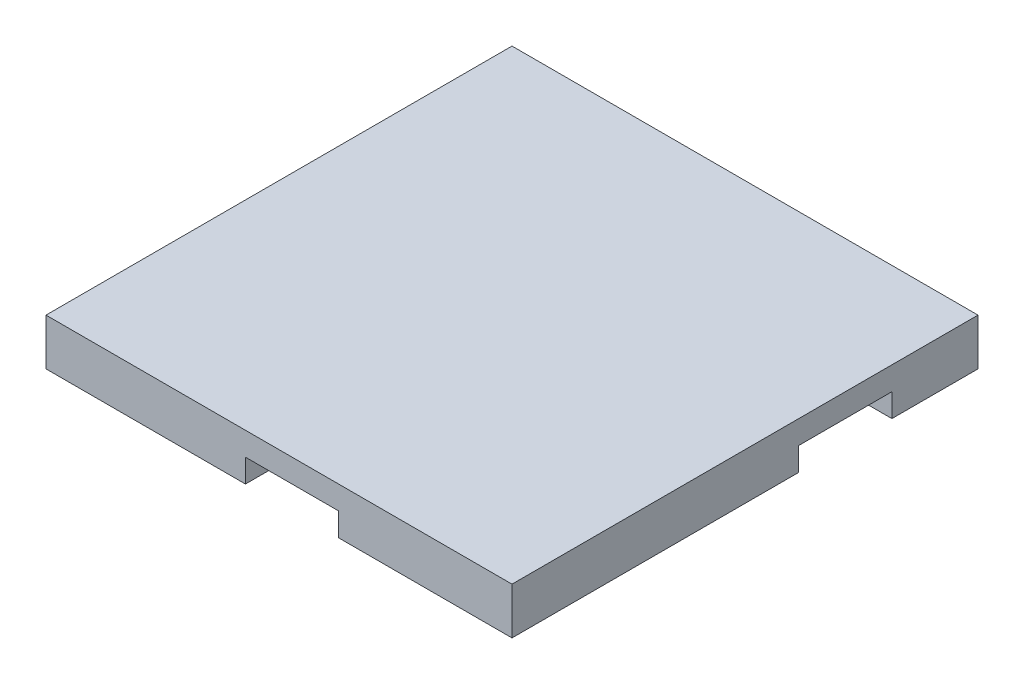
SolidWorks part; units mm, degrees
material "Rostfreier Chromstahl"
ref_plane "Ebene vorne" through (0, 0, 0) normal (0, 0, 1) x (1, 0, 0)
ref_plane "Ebene oben" through (0, 0, 0) normal (0, 1, 0) x (1, 0, 0)
ref_plane "Ebene rechts" through (0, 0, 0) normal (1, 0, 0) x (0, 0, -1)
sketch "Skizze1" plane through (0, 0, 0) normal (0, 1, 0) x (1, 0, 0)
  line L0 (0, 50) -> (0, 0) construction
  line L1 (-50, 50) -> (50, 50)
  line L2 (-50, 50) -> (-50, -50)
  line L3 (-50, -50) -> (50, -50)
  line L4 (50, 50) -> (50, -50)
  line L5 (0, 0) -> (50, 0) construction
  dimension "D1" = 100
  dimension "D2" = 100
extrude "Aufsatz-Linear austragen1" add sketch "Skizze1" along normal blind 10
sketch "Skizze3" plane through (0, 0, 0) normal (0, 1, 0) x (1, 0, 0)
  line L0 (50, 21.5216) -> (-25.561, 21.5216) construction
  line L1 (50, -50) -> (50, 50) construction
  line L2 (-25.561, 21.5216) -> (-25.561, -12.426) construction
  line L3 (-25.561, -12.426) -> (2.801, -12.426) construction
  line L4 (2.801, -12.426) -> (2.801, -50) construction
  line L5 (-50, -50) -> (50, -50) construction
  line L6 (50, 31.5216) -> (-35.561, 31.5216)
  line L7 (-35.561, 31.5216) -> (-35.561, -22.426)
  line L8 (-35.561, -22.426) -> (-7.199, -22.426)
  line L9 (-7.199, -22.426) -> (-7.199, -50)
  line L10 (50, 11.5216) -> (-15.561, 11.5216)
  line L11 (-15.561, 11.5216) -> (-15.561, -2.426)
  line L12 (-15.561, -2.426) -> (12.801, -2.426)
  line L13 (12.801, -2.426) -> (12.801, -50)
  arc A0 (50, 31.5216) -> (50, 11.5216) centre (50, 21.5216) cw
  arc A1 (-7.199, -50) -> (12.801, -50) centre (2.801, -50) ccw
  dimension "D1" = 10
  dimension "D2" = 10
extrude "Schnitt-Linear austragen1" cut sketch "Skizze3" along normal blind 5
